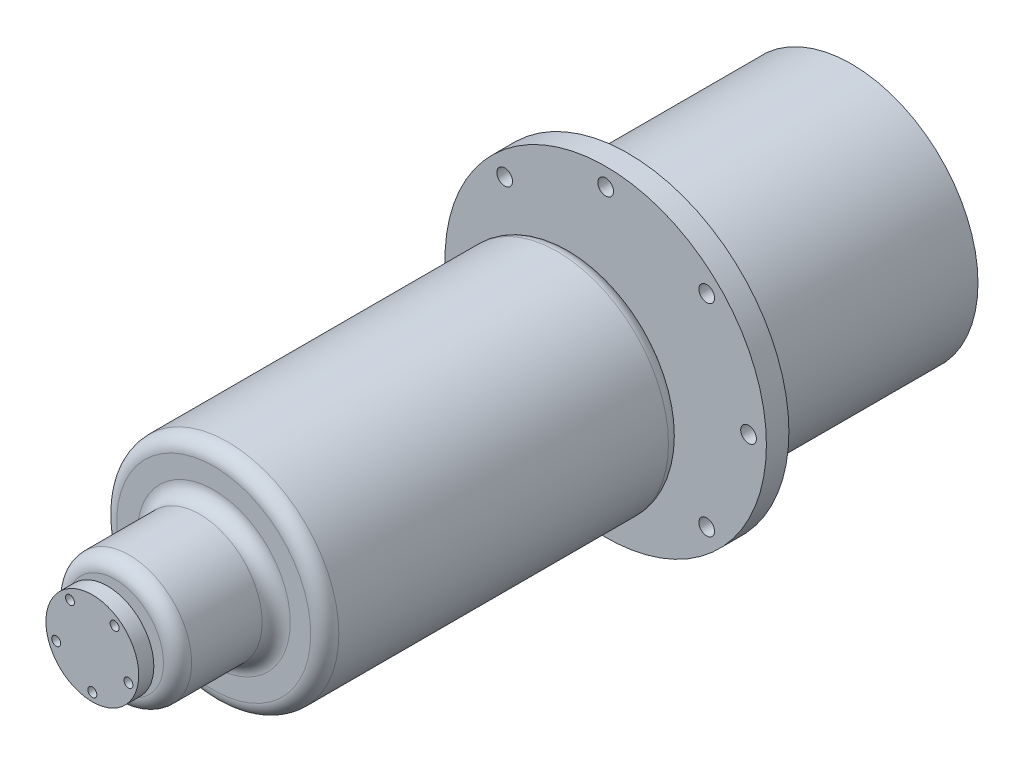
SolidWorks part; units mm, degrees
ref_plane "Front Plane" through (0, 0, 0) normal (0, 0, 1) x (1, 0, 0)
ref_plane "Top Plane" through (0, 0, 0) normal (0, 1, 0) x (1, 0, 0)
ref_plane "Right Plane" through (0, 0, 0) normal (1, 0, 0) x (0, 0, -1)
sketch "Sketch1" plane through (0, 0, 0) normal (0, 0, 1) x (1, 0, 0)
  line L0 (0, 84.8179) -> (0, -86.7057) construction
  line L1 (-97.3585, 0) -> (110.3037, 0) construction
  circle A0 centre (0, 0) radius 57.15
  dimension "D1" = 114.3
extrude "Extrude1" add sketch "Sketch1" along normal mid plane 8
sketch "Sketch3" plane through (0, 0, 4) normal (0, 0, 1) x (1, 0, 0)
  circle A0 centre (0, 0) radius 7.5
  dimension "D1" = 15
extrude "Extrude2" add sketch "Sketch3" along normal blind 12.166
sketch "Sketch4" plane through (0, 0, 16.166) normal (0, 0, 1) x (1, 0, 0)
  circle A0 centre (0, 0) radius 39.5
  dimension "D1" = 79
extrude "Extrude3" add sketch "Sketch4" along normal blind 127.24
sketch "Sketch5" plane through (0, 0, 143.406) normal (0, 0, 1) x (1, 0, 0)
  circle A0 centre (0, 0) radius 22.225
  dimension "D1" = 44.45
extrude "Extrude4" add sketch "Sketch5" along normal blind 35.0835
sketch "Sketch6" plane through (0, 0, 178.4895) normal (0, 0, 1) x (1, 0, 0)
  circle A0 centre (0, 0) radius 9.525
  dimension "D1" = 19.05
extrude "Extrude5" add sketch "Sketch6" along normal blind 2.7021
sketch "Sketch7" plane through (0, 0, 181.1915) normal (0, 0, 1) x (1, 0, 0)
  circle A0 centre (0, 0) radius 16.5
  dimension "D1" = 33
extrude "Extrude6" add sketch "Sketch7" along normal blind 5.3848
sketch "Sketch8" plane through (0, 0, 186.5763) normal (0, 0, 1) x (1, 0, 0)
  line L0 (0, 0) -> (-14.2331, 19.5901) construction
  line L1 (0, 0) -> (15.2254, 20.956) construction
  line L2 (0, 0) -> (18.3713, -5.9692) construction
  line L3 (0, 0) -> (0, -19.9096) construction
  line L4 (0, 0) -> (-20.1546, -6.5486) construction
  circle A0 centre (0, 0) radius 13.5 construction
  circle A1 centre (-7.9351, 10.9217) radius 1.6
  circle A2 centre (7.9351, 10.9217) radius 1.6
  circle A3 centre (12.8393, -4.1717) radius 1.6
  circle A4 centre (0, -13.5) radius 1.6
  circle A5 centre (-12.8393, -4.1717) radius 1.6
  dimension "D1" = 27
  dimension "D6" = 3.2
  dimension "D2" = 72
  dimension "D3" = 72
  dimension "D4" = 72
  dimension "D5" = 72
extrude "Cut-Extrude1" cut sketch "Sketch8" against normal blind 5.3848
sketch "Sketch10" plane through (0, 0, -4) normal (0, 0, -1) x (-1, 0, 0)
  line L0 (0, 62.7428) -> (0, -62.7428) construction
  line L1 (-61.7117, 0) -> (61.7117, 0) construction
  line L2 (46.601, 46.601) -> (-46.601, -46.601) construction
  line L3 (-47.2013, 47.2013) -> (47.2013, -47.2013) construction
  circle A1 centre (0, 0) radius 50.8 construction
  circle A2 centre (0, 50.8) radius 2.79
  circle A3 centre (35.921, 35.921) radius 2.79
  circle A4 centre (50.8, 0) radius 2.79
  circle A5 centre (35.921, -35.921) radius 2.79
  circle A6 centre (0, -50.8) radius 2.79
  circle A7 centre (-35.921, -35.921) radius 2.79
  circle A8 centre (-50.8, 0) radius 2.79
  circle A9 centre (-35.921, 35.921) radius 2.79
  dimension "D3" = 101.6
  dimension "D4" = 5.58
  dimension "D1" = 45
  dimension "D2" = 45
extrude "Cut-Extrude2" cut sketch "Sketch10" against normal up to surface (8 mm away) up to face at (57.15, 0, 4)
sketch "Sketch11" plane through (0, 0, -4) normal (0, 0, -1) x (-1, 0, 0)
  circle A0 centre (0, 0) radius 45
  dimension "D1" = 90
extrude "Extrude7" add sketch "Sketch11" along normal blind 79.4
fillet "Fillet1" radius 5 4 edges at (22.225, 0, 178.4895) (22.225, 0, 143.406) (39.5, 0, 16.166) (39.5, 0, 143.406)
